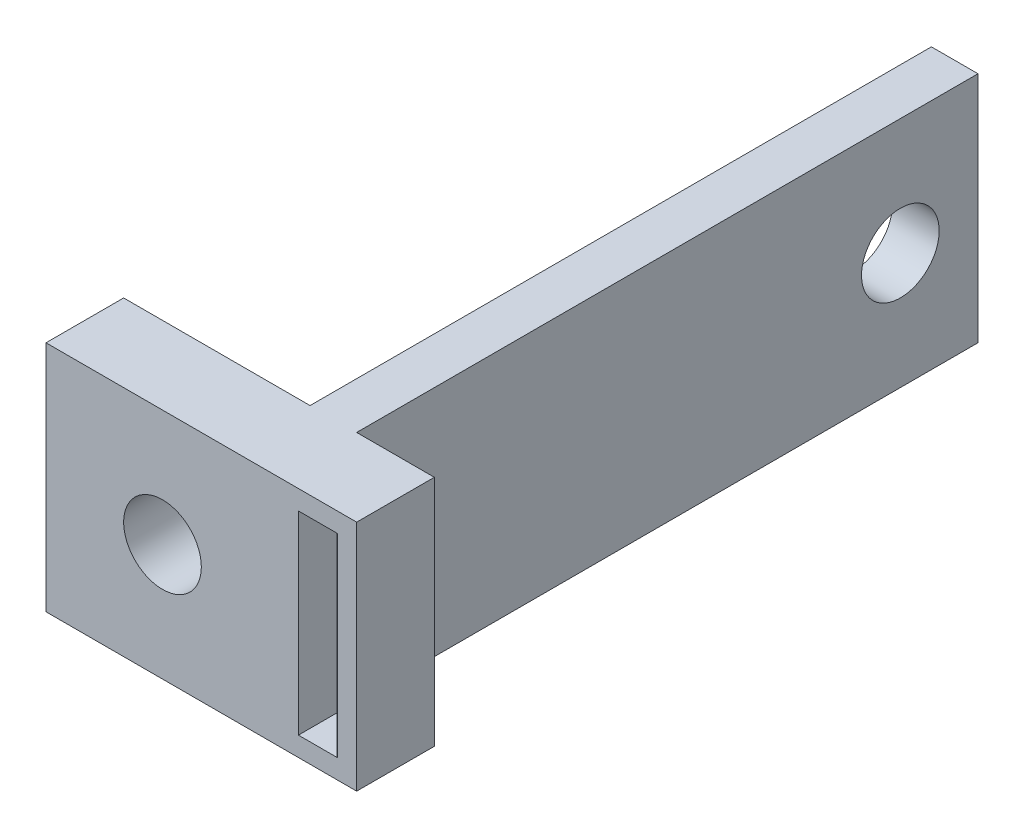
SolidWorks part; units mm, degrees
ref_plane "Front Plane" through (0, 0, 0) normal (0, 0, 1) x (1, 0, 0)
ref_plane "Top Plane" through (0, 0, 0) normal (0, 1, 0) x (1, 0, 0)
ref_plane "Right Plane" through (0, 0, 0) normal (1, 0, 0) x (0, 0, -1)
sketch "Sketch1" plane through (0, 0, 0) normal (0, 0, 1) x (1, 0, 0)
  line L1 (0, 0) -> (20, 0)
  line L2 (0, 0) -> (0, 15)
  line L3 (0, 15) -> (20, 15)
  line L4 (20, 0) -> (20, 15)
  dimension "D1" = 20
  dimension "D2" = 15
extrude "Boss-Extrude1" add sketch "Sketch1" along normal blind 5 contours L2 L3 L4 L1
sketch "Sketch2" plane through (0, 0, 5) normal (0, 0, 1) x (1, 0, 0)
  line L0 (0, 0) -> (0, 15) construction
  circle A0 centre (7.5, 7.5) radius 2.5
  point P4 (0, 7.5)
  dimension "D1" = 5
  dimension "D2" = 7.5
extrude "Cut-Extrude1" cut sketch "Sketch2" against normal blind 5
sketch "Sketch3" plane through (0, 0, 0) normal (0, 0, -1) x (-1, 0, 0)
  line L1 (0, 15) -> (-5, 15)
  line L5 (0, 15) -> (-20, 15) construction
  line L6 (-12, 15) -> (-15, 15)
  line L7 (-12, 15) -> (-12, 0)
  line L8 (-12, 0) -> (-15, 0)
  line L9 (-15, 15) -> (-15, 0)
  line L10 (0, 0) -> (-20, 0) construction
  line L11 (-20, 0) -> (-20, 15) construction
  dimension "D1" = 3
  dimension "D2" = 5
extrude "Boss-Extrude2" add sketch "Sketch3" along normal blind 40 contours L9 L8 L7 L6
sketch "Sketch4" plane through (15, 0, 0) normal (1, 0, 0) x (0, 0, -1)
  line L1 (40, 15) -> (40, 7.5) construction
  line L2 (40, 7.5) -> (40, 0) construction
  circle A0 centre (35, 7.5) radius 2.5
  dimension "D1" = 5
  dimension "D2" = 5
sketch "Sketch5" plane through (0, 0, 0) normal (0, 0, -1) x (-1, 0, 0)
  line L0 (-20, 0) -> (-20, 15) construction
  line L1 (-16.25, 13.75) -> (-18.75, 13.75)
  line L2 (-16.25, 13.75) -> (-16.25, 1.25)
  line L3 (-16.25, 1.25) -> (-18.75, 1.25)
  line L4 (-18.75, 13.75) -> (-18.75, 1.25)
  line L5 (-15, 15) -> (-20, 15) construction
  point P6 (-20, 7.5)
  point P7 (-18.75, 7.5)
  point P10 (-17.5, 15)
  point P11 (-17.5, 13.75)
  dimension "D1" = 12.5
  dimension "D2" = 2.5
extrude "Cut-Extrude3" cut sketch "Sketch5" against normal through all
extrude "Cut-Extrude4" cut sketch "Sketch4" against normal blind 10 contours A0
